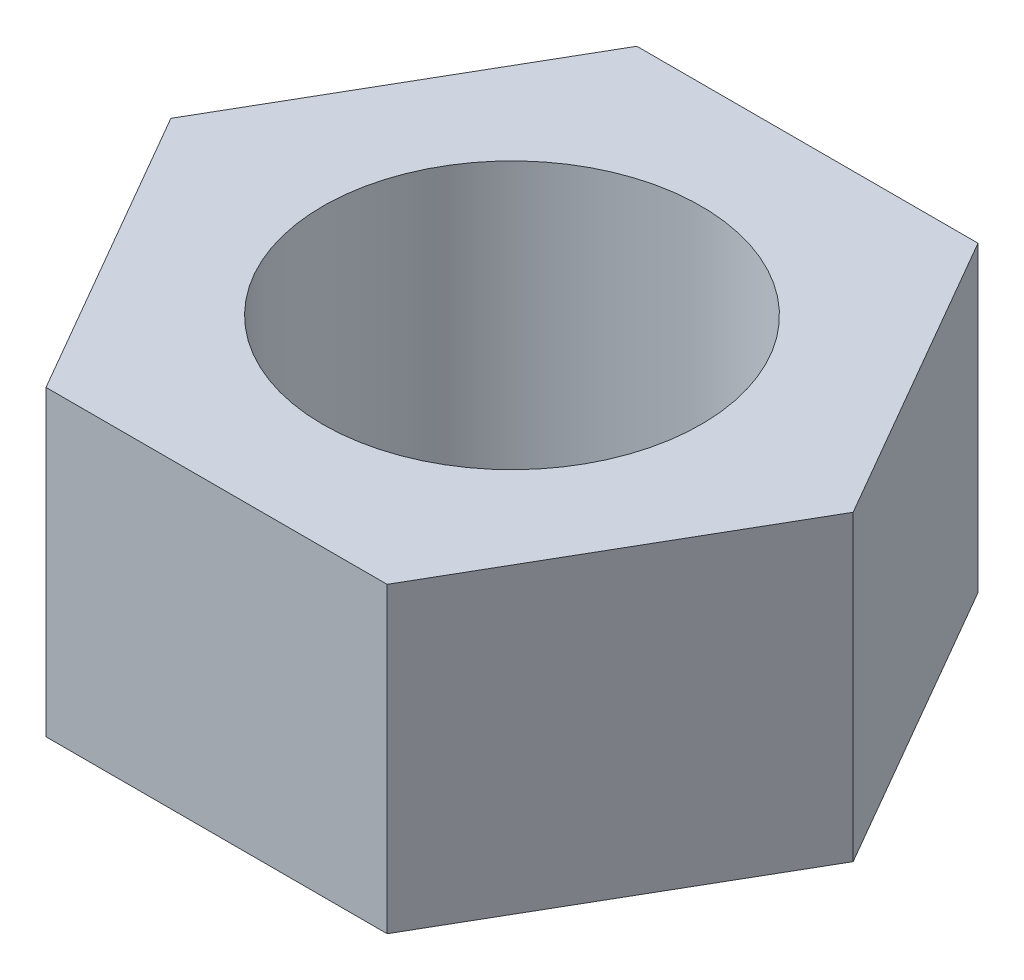
SolidWorks part; units mm, degrees
ref_plane "Front Plane" through (0, 0, 0) normal (0, 0, 1) x (1, 0, 0)
ref_plane "Top Plane" through (0, 0, 0) normal (0, 1, 0) x (1, 0, 0)
ref_plane "Right Plane" through (0, 0, 0) normal (1, 0, 0) x (0, 0, -1)
sketch "Sketch1" plane through (0, 0, 0) normal (0, 1, 0) x (1, 0, 0)
  line L0 (0, 0) -> (0, 3.9052) construction
  line L1 (-2.2547, 3.9052) -> (-4.5094, 0)
  line L2 (-4.5094, 0) -> (-2.2547, -3.9052)
  line L3 (-2.2547, -3.9052) -> (2.2547, -3.9052)
  line L4 (2.2547, -3.9052) -> (4.5094, 0)
  line L5 (4.5094, 0) -> (2.2547, 3.9052)
  line L6 (2.2547, 3.9052) -> (-2.2547, 3.9052)
  circle A0 centre (0, 0) radius 3.9052 construction
  circle A1 centre (0, 0) radius 2.5
  dimension "D2" = 5
  dimension "D1" = 7.8105
extrude "Boss-Extrude1" add sketch "Sketch1" along normal blind 4
